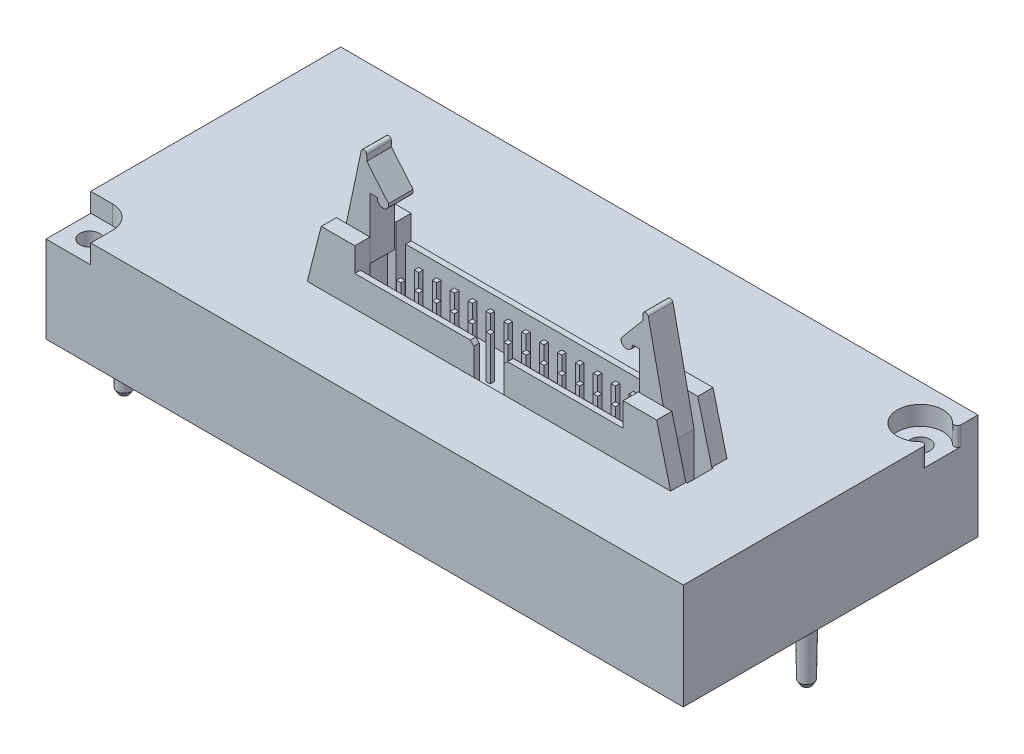
SolidWorks part; units mm, degrees
ref_plane "Front Plane" through (0, 0, 0) normal (0, 0, 1) x (1, 0, 0)
ref_plane "Top Plane" through (0, 0, 0) normal (0, 1, 0) x (1, 0, 0)
ref_plane "Right Plane" through (0, 0, 0) normal (1, 0, 0) x (0, 0, -1)
ref_plane "Plane1" through (0, 0, 0) normal (0, 1, 0) x (1, 0, 0)
sketch "Sketch1" plane through (0, 0, 0) normal (0, 1, 0) x (1, 0, 0)
  line L0 (-34.25, 15.25) -> (-34.25, -26.6)
  line L1 (-34.25, -26.6) -> (56.25, -26.6)
  line L2 (56.25, -26.6) -> (56.25, 15.25)
  line L3 (56.25, 15.25) -> (-34.25, 15.25)
  circle A0 centre (53.15, 10.15) radius 1.4
  circle A1 centre (-31.15, -23.5) radius 1.4
extrude "Boss-Extrude1" add sketch "Sketch1" along normal blind 15
ref_plane "Plane2" through (0, 15, 0) normal (0, 1, 0) x (1, 0, 0)
sketch "Sketch2" plane through (0, 15, 0) normal (0, 1, 0) x (1, 0, 0)
  line L0 (-40, 25) -> (-40, -35)
  line L1 (-40, -35) -> (65, -35)
  line L2 (65, -35) -> (65, 25)
  line L3 (65, 25) -> (-40, 25)
  line L4 (-34.25, 15.25) -> (-34.25, -20.25)
  line L5 (-34.25, -20.25) -> (-31.15, -20.25)
  line L6 (-27.9, -23.5) -> (-27.9, -26.6)
  line L7 (-27.9, -26.6) -> (56.25, -26.6)
  line L8 (56.25, -26.6) -> (56.25, 7.4477)
  line L9 (56.25, 12.8523) -> (56.25, 15.25)
  line L10 (56.25, 15.25) -> (-34.25, 15.25)
  arc A0 (-31.15, -20.25) -> (-27.9, -23.5) centre (-31.15, -23.5) cw
  arc A1 (56.25, 7.4477) -> (55.4033, 7.808) centre (55.75, 7.4477) ccw
  arc A2 (55.4033, 7.808) -> (55.4033, 12.492) centre (53.15, 10.15) cw
  arc A3 (55.4033, 12.492) -> (56.25, 12.8523) centre (55.75, 12.8523) ccw
extrude "Cut-Extrude1" cut sketch "Sketch2" against normal blind 2.7
ref_plane "Plane3" through (0, 0, 6) normal (0, 0, 1) x (1, 0, 0)
sketch "Sketch3" plane through (0, 0, 6) normal (0, 0, 1) x (1, 0, 0)
  line L0 (53.15, 0) -> (54.3, 0)
  line L1 (54.3, 0) -> (54.15, -8.4)
  line L2 (54.15, -8.4) -> (53.8, -9)
  line L3 (53.8, -9) -> (53.15, -9)
  line L4 (53.15, -9) -> (53.15, 0)
  line L5 (53.15, -9) -> (53.15, 0) construction
revolve "Revolve1" add sketch "Sketch3" angle 360 about L5
ref_plane "Plane4" through (0, 0, -5.25) normal (0, 0, 1) x (1, 0, 0)
sketch "Sketch4" plane through (0, 0, -5.25) normal (0, 0, 1) x (1, 0, 0)
  line L0 (-31.15, 0) -> (-30, 0)
  line L1 (-30, 0) -> (-30.15, -8.4)
  line L2 (-30.15, -8.4) -> (-30.5, -9)
  line L3 (-30.5, -9) -> (-31.15, -9)
  line L4 (-31.15, -9) -> (-31.15, 0)
  line L5 (-31.15, -9) -> (-31.15, 0) construction
revolve "Revolve2" add sketch "Sketch4" angle 360 about L5
ref_plane "Plane5" through (0, 0, 18.6) normal (0, 0, 1) x (1, 0, 0)
sketch "Sketch5" plane through (0, 0, 18.6) normal (0, 0, 1) x (1, 0, 0)
  line L0 (-31.15, 0) -> (-30, 0)
  line L1 (-30, 0) -> (-30.15, -8.4)
  line L2 (-30.15, -8.4) -> (-30.5, -9)
  line L3 (-30.5, -9) -> (-31.15, -9)
  line L4 (-31.15, -9) -> (-31.15, 0)
  line L5 (-31.15, -9) -> (-31.15, 0) construction
revolve "Revolve3" add sketch "Sketch5" angle 360 about L5
ref_plane "Plane6" through (0, 0, 11.95) normal (0, 0, 1) x (1, 0, 0)
sketch "Sketch6" plane through (0, 0, 11.95) normal (0, 0, 1) x (1, 0, 0)
  line L0 (-8.225, 13.35) -> (-8.225, 5.35)
  line L1 (-8.225, 5.35) -> (44.225, 5.35)
  line L2 (44.225, 5.35) -> (44.225, 13.35)
  line L3 (44.225, 13.35) -> (41.815, 22.75)
  line L4 (41.815, 22.75) -> (37.05, 22.75)
  line L5 (37.05, 22.75) -> (37.05, 19.35)
  line L6 (37.05, 19.35) -> (-1.05, 19.35)
  line L7 (-1.05, 19.35) -> (-1.05, 22.75)
  line L8 (-1.05, 22.75) -> (-5.815, 22.75)
  line L9 (-5.815, 22.75) -> (-8.225, 13.35)
extrude "Boss-Extrude2" add sketch "Sketch6" against normal blind 4 and the other way blind 4
ref_plane "Plane7" through (0, 19.35, 0) normal (0, 1, 0) x (1, 0, 0)
sketch "Sketch7" plane through (0, 19.35, 0) normal (0, 1, 0) x (1, 0, 0)
  line L0 (-1.05, -8.735) -> (-1.05, -15.165)
  line L1 (-1.05, -15.165) -> (37.05, -15.165)
  line L2 (37.05, -15.165) -> (37.05, -8.735)
  line L3 (37.05, -8.735) -> (-1.05, -8.735)
extrude "Cut-Extrude2" cut sketch "Sketch7" against normal blind 6.4 and the other way blind 6.4
ref_plane "Plane8" through (0, 0, 15.95) normal (0, 0, 1) x (1, 0, 0)
sketch "Sketch8" plane through (0, 0, 15.95) normal (0, 0, 1) x (1, 0, 0)
  line L0 (15.35, 19.35) -> (15.85, 18.85)
  line L1 (15.85, 18.85) -> (15.85, 13.45)
  line L2 (15.85, 13.45) -> (16.35, 12.95)
  line L3 (16.35, 12.95) -> (19.65, 12.95)
  line L4 (19.65, 12.95) -> (20.15, 13.45)
  line L5 (20.15, 13.45) -> (20.15, 18.85)
  line L6 (20.15, 18.85) -> (20.65, 19.35)
  line L7 (20.65, 19.35) -> (15.35, 19.35)
extrude "Cut-Extrude3" cut sketch "Sketch8" against normal blind 1
ref_plane "Plane9" through (37, 0, 0) normal (1, 0, 0) x (0, 0, -1)
sketch "Sketch9" plane through (37, 0, 0) normal (1, 0, 0) x (0, 0, -1)
  line L0 (-13.79, 9.75) -> (-10.11, 9.75)
  line L1 (-10.11, 9.75) -> (-10.11, 22.75)
  line L2 (-10.11, 22.75) -> (-13.79, 22.75)
  line L3 (-13.79, 22.75) -> (-13.79, 9.75)
extrude "Cut-Extrude4" cut sketch "Sketch9" along normal blind 7
ref_plane "Plane10" through (-1.05, 0, 0) normal (1, 0, 0) x (0, 0, -1)
sketch "Sketch10" plane through (-1.05, 0, 0) normal (1, 0, 0) x (0, 0, -1)
  line L0 (-13.79, 9.75) -> (-10.11, 9.75)
  line L1 (-10.11, 9.75) -> (-10.11, 22.75)
  line L2 (-10.11, 22.75) -> (-13.79, 22.75)
  line L3 (-13.79, 22.75) -> (-13.79, 9.75)
extrude "Cut-Extrude5" cut sketch "Sketch10" against normal blind 7
ref_plane "Plane11" through (0, 0, 11.95) normal (0, 0, 1) x (1, 0, 0)
sketch "Sketch11" plane through (0, 0, 11.95) normal (0, 0, 1) x (1, 0, 0)
  circle A0 centre (40.225, 15.21) radius 0.5
extrude "Boss-Extrude3" add sketch "Sketch11" against normal blind 3 and the other way blind 3
ref_plane "Plane12" through (0, 0, 11.95) normal (0, 0, 1) x (1, 0, 0)
sketch "Sketch12" plane through (0, 0, 11.95) normal (0, 0, 1) x (1, 0, 0)
  circle A0 centre (-4.225, 15.21) radius 0.5
extrude "Boss-Extrude4" add sketch "Sketch12" against normal blind 3 and the other way blind 3
ref_plane "Plane13" through (0, 0, 11.95) normal (0, 0, 1) x (1, 0, 0)
sketch "Sketch13" plane through (0, 0, 11.95) normal (0, 0, 1) x (1, 0, 0)
  line L0 (36.1002, 28.0445) -> (37.155, 28.0445)
  line L1 (37.155, 28.0445) -> (37.155, 19.373)
  line L2 (37.155, 19.373) -> (38.155, 19.373)
  line L3 (38.155, 19.373) -> (38.155, 11.9703)
  line L4 (41.385, 11.9703) -> (41.385, 18.5122)
  line L5 (41.385, 18.5122) -> (38.3913, 32.633)
  line L6 (37.6, 32.55) -> (37.6, 31.75)
  line L7 (37.6, 31.75) -> (34.5146, 28.073)
  arc A0 (34.5146, 28.073) -> (36.1002, 28.0445) centre (35.305, 27.9259) ccw
  arc A1 (38.155, 11.9703) -> (41.385, 11.9703) centre (39.77, 13.15) ccw
  arc A2 (38.3913, 32.633) -> (37.6, 32.55) centre (38, 32.55) ccw
extrude "Boss-Extrude5" add sketch "Sketch13" against normal blind 1.75 and the other way blind 1.75
ref_plane "Plane14" through (0, 0, 11.95) normal (0, 0, 1) x (1, 0, 0)
sketch "Sketch14" plane through (0, 0, 11.95) normal (0, 0, 1) x (1, 0, 0)
  line L0 (-5.385, 18.5122) -> (-5.385, 11.9703)
  line L1 (-2.155, 11.9703) -> (-2.155, 19.373)
  line L2 (-2.155, 19.373) -> (-1.155, 19.373)
  line L3 (-1.155, 19.373) -> (-1.155, 28.0445)
  line L4 (-1.155, 28.0445) -> (-0.1002, 28.0445)
  line L5 (1.4854, 28.073) -> (-1.6, 31.75)
  line L6 (-1.6, 31.75) -> (-1.6, 32.55)
  line L7 (-2.3913, 32.633) -> (-5.385, 18.5122)
  arc A0 (-5.385, 11.9703) -> (-2.155, 11.9703) centre (-3.77, 13.15) ccw
  arc A1 (-0.1002, 28.0445) -> (1.4854, 28.073) centre (0.695, 27.9259) ccw
  arc A2 (-1.6, 32.55) -> (-2.3913, 32.633) centre (-2, 32.55) ccw
extrude "Boss-Extrude6" add sketch "Sketch14" against normal blind 1.75 and the other way blind 1.75
ref_plane "Plane15" through (0, 12.95, 0) normal (0, 1, 0) x (1, 0, 0)
sketch "Sketch15" plane through (0, 12.95, 0) normal (0, 1, 0) x (1, 0, 0)
  line L0 (2.45, -12.91) -> (2.45, -13.53)
  line L1 (2.45, -13.53) -> (3.07, -13.53)
  line L2 (3.07, -13.53) -> (3.07, -12.91)
  line L3 (3.07, -12.91) -> (2.45, -12.91)
extrude "Boss-Extrude7" add sketch "Sketch15" along normal blind 6.1
ref_plane "Plane16" through (0, 12.95, 0) normal (0, 1, 0) x (1, 0, 0)
sketch "Sketch16" plane through (0, 12.95, 0) normal (0, 1, 0) x (1, 0, 0)
  line L0 (4.99, -12.91) -> (4.99, -13.53)
  line L1 (4.99, -13.53) -> (5.61, -13.53)
  line L2 (5.61, -13.53) -> (5.61, -12.91)
  line L3 (5.61, -12.91) -> (4.99, -12.91)
extrude "Boss-Extrude8" add sketch "Sketch16" along normal blind 6.1
ref_plane "Plane17" through (0, 12.95, 0) normal (0, 1, 0) x (1, 0, 0)
sketch "Sketch17" plane through (0, 12.95, 0) normal (0, 1, 0) x (1, 0, 0)
  line L0 (7.53, -12.91) -> (7.53, -13.53)
  line L1 (7.53, -13.53) -> (8.15, -13.53)
  line L2 (8.15, -13.53) -> (8.15, -12.91)
  line L3 (8.15, -12.91) -> (7.53, -12.91)
extrude "Boss-Extrude9" add sketch "Sketch17" along normal blind 6.1
ref_plane "Plane18" through (0, 12.95, 0) normal (0, 1, 0) x (1, 0, 0)
sketch "Sketch18" plane through (0, 12.95, 0) normal (0, 1, 0) x (1, 0, 0)
  line L0 (10.07, -12.91) -> (10.07, -13.53)
  line L1 (10.07, -13.53) -> (10.69, -13.53)
  line L2 (10.69, -13.53) -> (10.69, -12.91)
  line L3 (10.69, -12.91) -> (10.07, -12.91)
extrude "Boss-Extrude10" add sketch "Sketch18" along normal blind 6.1
ref_plane "Plane19" through (0, 12.95, 0) normal (0, 1, 0) x (1, 0, 0)
sketch "Sketch19" plane through (0, 12.95, 0) normal (0, 1, 0) x (1, 0, 0)
  line L0 (12.61, -12.91) -> (12.61, -13.53)
  line L1 (12.61, -13.53) -> (13.23, -13.53)
  line L2 (13.23, -13.53) -> (13.23, -12.91)
  line L3 (13.23, -12.91) -> (12.61, -12.91)
extrude "Boss-Extrude11" add sketch "Sketch19" along normal blind 6.1
ref_plane "Plane20" through (0, 12.95, 0) normal (0, 1, 0) x (1, 0, 0)
sketch "Sketch20" plane through (0, 12.95, 0) normal (0, 1, 0) x (1, 0, 0)
  line L0 (15.15, -12.91) -> (15.15, -13.53)
  line L1 (15.15, -13.53) -> (15.77, -13.53)
  line L2 (15.77, -13.53) -> (15.77, -12.91)
  line L3 (15.77, -12.91) -> (15.15, -12.91)
extrude "Boss-Extrude12" add sketch "Sketch20" along normal blind 6.1
ref_plane "Plane21" through (0, 12.95, 0) normal (0, 1, 0) x (1, 0, 0)
sketch "Sketch21" plane through (0, 12.95, 0) normal (0, 1, 0) x (1, 0, 0)
  line L0 (17.69, -12.91) -> (17.69, -13.53)
  line L1 (17.69, -13.53) -> (18.31, -13.53)
  line L2 (18.31, -13.53) -> (18.31, -12.91)
  line L3 (18.31, -12.91) -> (17.69, -12.91)
extrude "Boss-Extrude13" add sketch "Sketch21" along normal blind 6.1
ref_plane "Plane22" through (0, 12.95, 0) normal (0, 1, 0) x (1, 0, 0)
sketch "Sketch22" plane through (0, 12.95, 0) normal (0, 1, 0) x (1, 0, 0)
  line L0 (20.23, -12.91) -> (20.23, -13.53)
  line L1 (20.23, -13.53) -> (20.85, -13.53)
  line L2 (20.85, -13.53) -> (20.85, -12.91)
  line L3 (20.85, -12.91) -> (20.23, -12.91)
extrude "Boss-Extrude14" add sketch "Sketch22" along normal blind 6.1
ref_plane "Plane23" through (0, 12.95, 0) normal (0, 1, 0) x (1, 0, 0)
sketch "Sketch23" plane through (0, 12.95, 0) normal (0, 1, 0) x (1, 0, 0)
  line L0 (22.77, -12.91) -> (22.77, -13.53)
  line L1 (22.77, -13.53) -> (23.39, -13.53)
  line L2 (23.39, -13.53) -> (23.39, -12.91)
  line L3 (23.39, -12.91) -> (22.77, -12.91)
extrude "Boss-Extrude15" add sketch "Sketch23" along normal blind 6.1
ref_plane "Plane24" through (0, 12.95, 0) normal (0, 1, 0) x (1, 0, 0)
sketch "Sketch24" plane through (0, 12.95, 0) normal (0, 1, 0) x (1, 0, 0)
  line L0 (25.31, -12.91) -> (25.31, -13.53)
  line L1 (25.31, -13.53) -> (25.93, -13.53)
  line L2 (25.93, -13.53) -> (25.93, -12.91)
  line L3 (25.93, -12.91) -> (25.31, -12.91)
extrude "Boss-Extrude16" add sketch "Sketch24" along normal blind 6.1
ref_plane "Plane25" through (0, 12.95, 0) normal (0, 1, 0) x (1, 0, 0)
sketch "Sketch25" plane through (0, 12.95, 0) normal (0, 1, 0) x (1, 0, 0)
  line L0 (27.85, -12.91) -> (27.85, -13.53)
  line L1 (27.85, -13.53) -> (28.47, -13.53)
  line L2 (28.47, -13.53) -> (28.47, -12.91)
  line L3 (28.47, -12.91) -> (27.85, -12.91)
extrude "Boss-Extrude17" add sketch "Sketch25" along normal blind 6.1
ref_plane "Plane26" through (0, 12.95, 0) normal (0, 1, 0) x (1, 0, 0)
sketch "Sketch26" plane through (0, 12.95, 0) normal (0, 1, 0) x (1, 0, 0)
  line L0 (30.39, -12.91) -> (30.39, -13.53)
  line L1 (30.39, -13.53) -> (31.01, -13.53)
  line L2 (31.01, -13.53) -> (31.01, -12.91)
  line L3 (31.01, -12.91) -> (30.39, -12.91)
extrude "Boss-Extrude18" add sketch "Sketch26" along normal blind 6.1
ref_plane "Plane27" through (0, 12.95, 0) normal (0, 1, 0) x (1, 0, 0)
sketch "Sketch27" plane through (0, 12.95, 0) normal (0, 1, 0) x (1, 0, 0)
  line L0 (32.93, -12.91) -> (32.93, -13.53)
  line L1 (32.93, -13.53) -> (33.55, -13.53)
  line L2 (33.55, -13.53) -> (33.55, -12.91)
  line L3 (33.55, -12.91) -> (32.93, -12.91)
extrude "Boss-Extrude19" add sketch "Sketch27" along normal blind 6.1
ref_plane "Plane28" through (0, 12.95, 0) normal (0, 1, 0) x (1, 0, 0)
sketch "Sketch28" plane through (0, 12.95, 0) normal (0, 1, 0) x (1, 0, 0)
  line L0 (2.45, -10.37) -> (2.45, -10.99)
  line L1 (2.45, -10.99) -> (3.07, -10.99)
  line L2 (3.07, -10.99) -> (3.07, -10.37)
  line L3 (3.07, -10.37) -> (2.45, -10.37)
extrude "Boss-Extrude20" add sketch "Sketch28" along normal blind 6.1
ref_plane "Plane29" through (0, 12.95, 0) normal (0, 1, 0) x (1, 0, 0)
sketch "Sketch29" plane through (0, 12.95, 0) normal (0, 1, 0) x (1, 0, 0)
  line L0 (4.99, -10.37) -> (4.99, -10.99)
  line L1 (4.99, -10.99) -> (5.61, -10.99)
  line L2 (5.61, -10.99) -> (5.61, -10.37)
  line L3 (5.61, -10.37) -> (4.99, -10.37)
extrude "Boss-Extrude21" add sketch "Sketch29" along normal blind 6.1
ref_plane "Plane30" through (0, 12.95, 0) normal (0, 1, 0) x (1, 0, 0)
sketch "Sketch30" plane through (0, 12.95, 0) normal (0, 1, 0) x (1, 0, 0)
  line L0 (7.53, -10.37) -> (7.53, -10.99)
  line L1 (7.53, -10.99) -> (8.15, -10.99)
  line L2 (8.15, -10.99) -> (8.15, -10.37)
  line L3 (8.15, -10.37) -> (7.53, -10.37)
extrude "Boss-Extrude22" add sketch "Sketch30" along normal blind 6.1
ref_plane "Plane31" through (0, 12.95, 0) normal (0, 1, 0) x (1, 0, 0)
sketch "Sketch31" plane through (0, 12.95, 0) normal (0, 1, 0) x (1, 0, 0)
  line L0 (10.07, -10.37) -> (10.07, -10.99)
  line L1 (10.07, -10.99) -> (10.69, -10.99)
  line L2 (10.69, -10.99) -> (10.69, -10.37)
  line L3 (10.69, -10.37) -> (10.07, -10.37)
extrude "Boss-Extrude23" add sketch "Sketch31" along normal blind 6.1
ref_plane "Plane32" through (0, 12.95, 0) normal (0, 1, 0) x (1, 0, 0)
sketch "Sketch32" plane through (0, 12.95, 0) normal (0, 1, 0) x (1, 0, 0)
  line L0 (12.61, -10.37) -> (12.61, -10.99)
  line L1 (12.61, -10.99) -> (13.23, -10.99)
  line L2 (13.23, -10.99) -> (13.23, -10.37)
  line L3 (13.23, -10.37) -> (12.61, -10.37)
extrude "Boss-Extrude24" add sketch "Sketch32" along normal blind 6.1
ref_plane "Plane33" through (0, 12.95, 0) normal (0, 1, 0) x (1, 0, 0)
sketch "Sketch33" plane through (0, 12.95, 0) normal (0, 1, 0) x (1, 0, 0)
  line L0 (15.15, -10.37) -> (15.15, -10.99)
  line L1 (15.15, -10.99) -> (15.77, -10.99)
  line L2 (15.77, -10.99) -> (15.77, -10.37)
  line L3 (15.77, -10.37) -> (15.15, -10.37)
extrude "Boss-Extrude25" add sketch "Sketch33" along normal blind 6.1
ref_plane "Plane34" through (0, 12.95, 0) normal (0, 1, 0) x (1, 0, 0)
sketch "Sketch34" plane through (0, 12.95, 0) normal (0, 1, 0) x (1, 0, 0)
  line L0 (17.69, -10.37) -> (17.69, -10.99)
  line L1 (17.69, -10.99) -> (18.31, -10.99)
  line L2 (18.31, -10.99) -> (18.31, -10.37)
  line L3 (18.31, -10.37) -> (17.69, -10.37)
extrude "Boss-Extrude26" add sketch "Sketch34" along normal blind 6.1
ref_plane "Plane35" through (0, 12.95, 0) normal (0, 1, 0) x (1, 0, 0)
sketch "Sketch35" plane through (0, 12.95, 0) normal (0, 1, 0) x (1, 0, 0)
  line L0 (20.23, -10.37) -> (20.23, -10.99)
  line L1 (20.23, -10.99) -> (20.85, -10.99)
  line L2 (20.85, -10.99) -> (20.85, -10.37)
  line L3 (20.85, -10.37) -> (20.23, -10.37)
extrude "Boss-Extrude27" add sketch "Sketch35" along normal blind 6.1
ref_plane "Plane36" through (0, 12.95, 0) normal (0, 1, 0) x (1, 0, 0)
sketch "Sketch36" plane through (0, 12.95, 0) normal (0, 1, 0) x (1, 0, 0)
  line L0 (22.77, -10.37) -> (22.77, -10.99)
  line L1 (22.77, -10.99) -> (23.39, -10.99)
  line L2 (23.39, -10.99) -> (23.39, -10.37)
  line L3 (23.39, -10.37) -> (22.77, -10.37)
extrude "Boss-Extrude28" add sketch "Sketch36" along normal blind 6.1
ref_plane "Plane37" through (0, 12.95, 0) normal (0, 1, 0) x (1, 0, 0)
sketch "Sketch37" plane through (0, 12.95, 0) normal (0, 1, 0) x (1, 0, 0)
  line L0 (25.31, -10.37) -> (25.31, -10.99)
  line L1 (25.31, -10.99) -> (25.93, -10.99)
  line L2 (25.93, -10.99) -> (25.93, -10.37)
  line L3 (25.93, -10.37) -> (25.31, -10.37)
extrude "Boss-Extrude29" add sketch "Sketch37" along normal blind 6.1
ref_plane "Plane38" through (0, 12.95, 0) normal (0, 1, 0) x (1, 0, 0)
sketch "Sketch38" plane through (0, 12.95, 0) normal (0, 1, 0) x (1, 0, 0)
  line L0 (27.85, -10.37) -> (27.85, -10.99)
  line L1 (27.85, -10.99) -> (28.47, -10.99)
  line L2 (28.47, -10.99) -> (28.47, -10.37)
  line L3 (28.47, -10.37) -> (27.85, -10.37)
extrude "Boss-Extrude30" add sketch "Sketch38" along normal blind 6.1
ref_plane "Plane39" through (0, 12.95, 0) normal (0, 1, 0) x (1, 0, 0)
sketch "Sketch39" plane through (0, 12.95, 0) normal (0, 1, 0) x (1, 0, 0)
  line L0 (30.39, -10.37) -> (30.39, -10.99)
  line L1 (30.39, -10.99) -> (31.01, -10.99)
  line L2 (31.01, -10.99) -> (31.01, -10.37)
  line L3 (31.01, -10.37) -> (30.39, -10.37)
extrude "Boss-Extrude31" add sketch "Sketch39" along normal blind 6.1
ref_plane "Plane40" through (0, 12.95, 0) normal (0, 1, 0) x (1, 0, 0)
sketch "Sketch40" plane through (0, 12.95, 0) normal (0, 1, 0) x (1, 0, 0)
  line L0 (32.93, -10.37) -> (32.93, -10.99)
  line L1 (32.93, -10.99) -> (33.55, -10.99)
  line L2 (33.55, -10.99) -> (33.55, -10.37)
  line L3 (33.55, -10.37) -> (32.93, -10.37)
extrude "Boss-Extrude32" add sketch "Sketch40" along normal blind 6.1
